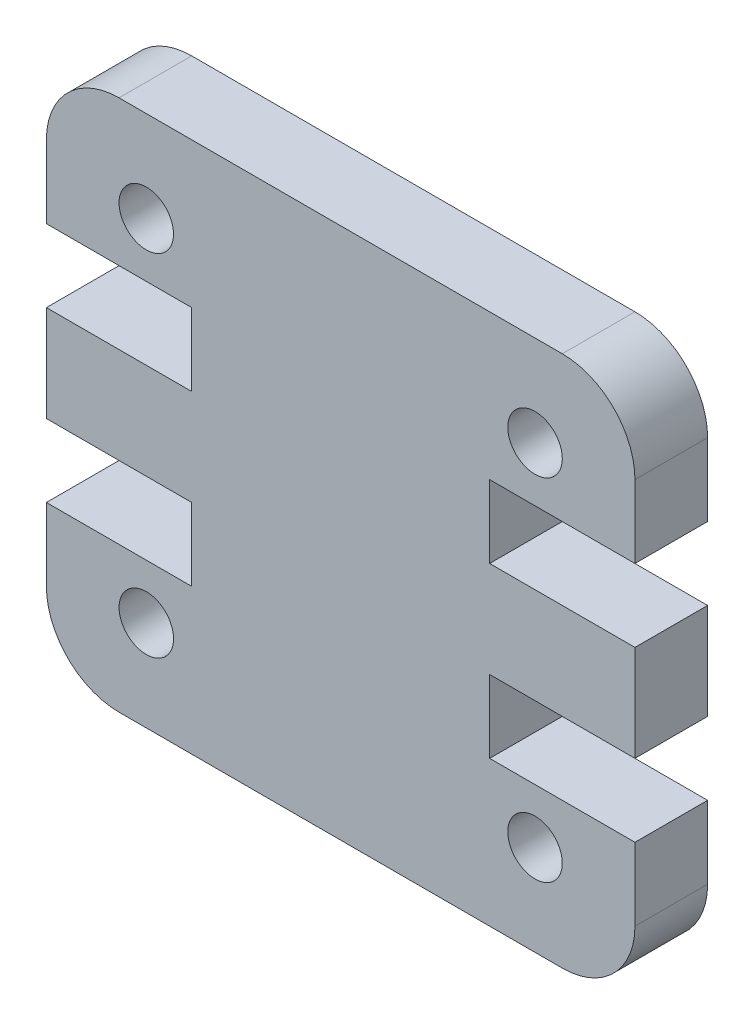
SolidWorks part; units mm, degrees
ref_plane "Front Plane" through (0, 0, 0) normal (0, 0, 1) x (1, 0, 0)
ref_plane "Top Plane" through (0, 0, 0) normal (0, 1, 0) x (1, 0, 0)
ref_plane "Right Plane" through (0, 0, 0) normal (1, 0, 0) x (0, 0, -1)
sketch "Sketch1" plane through (0, 0, 0) normal (0, 0, 1) x (1, 0, 0)
  line L0 (8.1, 14.645) -> (8.1, 0) construction
  line L1 (0, 7.3225) -> (16.2, 7.3225) construction
  line L2 (16.2, 4) -> (16.2, 2)
  line L3 (12.2, 6) -> (12.2, 4)
  line L4 (16.2, 6) -> (12.2, 6)
  line L5 (12.2, 4) -> (16.2, 4)
  line L6 (16.2, 8.645) -> (16.2, 6)
  line L7 (0, 10.645) -> (0, 12.645)
  line L8 (4, 8.645) -> (4, 10.645)
  line L9 (0, 8.645) -> (4, 8.645)
  line L10 (4, 10.645) -> (0, 10.645)
  line L11 (2, 14.645) -> (14.2, 14.645)
  line L12 (0, 8.645) -> (0, 6)
  line L13 (12.2, 10.645) -> (16.2, 10.645)
  line L14 (16.2, 8.645) -> (12.2, 8.645)
  line L15 (12.2, 8.645) -> (12.2, 10.645)
  line L16 (16.2, 10.645) -> (16.2, 12.645)
  line L19 (2, 0) -> (14.2, 0)
  line L21 (4, 4) -> (0, 4)
  line L22 (0, 6) -> (4, 6)
  line L23 (4, 6) -> (4, 4)
  line L24 (0, 4) -> (0, 2)
  circle A0 centre (13.45, 2.5) radius 0.75
  arc A1 (16.2, 2) -> (14.2, 0) centre (14.2, 2) cw
  circle A2 centre (2.75, 12.145) radius 0.75
  arc A3 (0, 12.645) -> (2, 14.645) centre (2, 12.645) cw
  arc A4 (16.2, 12.645) -> (14.2, 14.645) centre (14.2, 12.645) ccw
  circle A5 centre (13.45, 12.145) radius 0.75
  arc A11 (0, 2) -> (2, 0) centre (2, 2) ccw
  circle A13 centre (2.75, 2.5) radius 0.75
  point P14 (8.1, 7.3225)
  dimension "D1" = 1.5
  dimension "D2" = 2
  dimension "D3" = 2.75
  dimension "D4" = 8.1
  dimension "D5" = 2.5
  dimension "D6" = 7.3225
extrude "Boss-Extrude1" add sketch "Sketch1" along normal blind 2
equation "\"D4@Sketch1\"= \"fingerWidth@parametersSketch@prostheticParameters.SLDPRT\" / 2'MIP width"
equation "\"D6@Sketch1\"= ( \"HL@parametersSketch@prostheticParameters.SLDPRT\" * 0.117 - 4 - 3 ) / 2 'MIP length - Sil. Sht DIP - Sil. Sht MIP"
